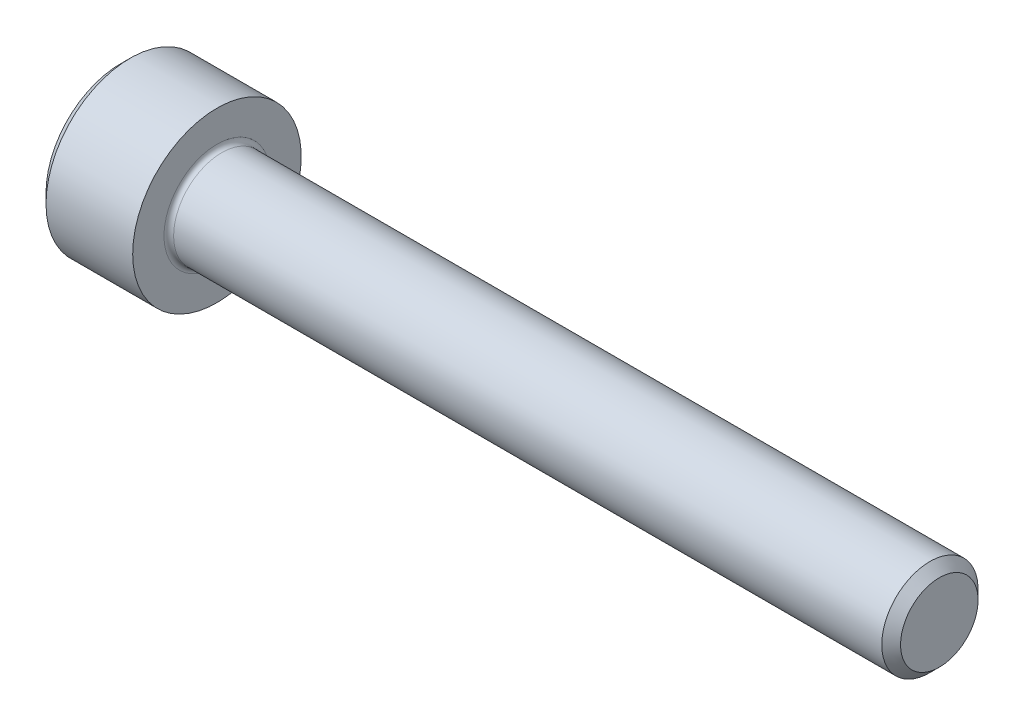
SolidWorks part; units mm, degrees
revolve "Base-Revolve" add sketch "BodySke"
sketch "BodySke" plane through (0, 0, 0) normal (0, 0, 1) x (1, 0, 0)
  line L0 (0, 0) -> (0, 3.1)
  line L1 (0.4, 3.5) -> (4, 3.5)
  line L2 (4, 3.5) -> (4, 2)
  line L3 (4, 2) -> (33.61, 2)
  line L4 (34, 1.61) -> (34, 0)
  line L5 (34, 0) -> (0, 0)
  line L6 (-31.75, 0) -> (127, 0) construction
  line L7 (0, 3.1) -> (0.4, 3.5)
  line L8 (34, 1.61) -> (33.61, 2)
  line L9 (0, -3.1) -> (0.4, -3.5) construction
  line L10 (34, -1.61) -> (33.61, -2) construction
  line L11 (4.7, 9.525) -> (4.7, 3.175) construction
  line L12 (4, 9.525) -> (4, 3.175) construction
  line L13 (-16, 9.525) -> (-16, 3.175) construction
  dimension "Diameter" = 4
  dimension "Head_ht" = 4
  dimension "Length" = 30
  dimension "Body_ch_ang" = 45
  dimension "Head_dia" = 7
  dimension "Head_ch_ang" = 45
  dimension "Minor_dia" = 3.22
  dimension "Advance" = 0.7
  dimension "Thread_nom" = 30
  dimension "Thread_length" = 50
  dimension "Head_ch_ht" = 0.4
cosmetic thread "ThreadCosmetic" [suppressed]
fillet "Fillet1" radius 0.2 1 edges at (4, 0, 2)
ref_plane "Plane1" through (0, 0, 0) normal (0, 0, 1) x (1, 0, 0)
ref_plane "Plane2" through (0, 0, 0) normal (0, 1, 0) x (1, 0, 0)
ref_plane "Plane3" through (0, 0, 0) normal (1, 0, 0) x (0, 0, -1)
other "Configuration Table"
sketch "Sketch2" plane through (0, 0, 0) normal (0, 0, 1) x (1, 0, 0)
  line L0 (0, 1.5355) -> (2, 1.5355)
  line L1 (2, 1.5355) -> (2.8865, 0)
  line L2 (-31.75, 0) -> (127, 0) construction
  line L3 (2.8865, 0) -> (0, 0)
  line L4 (0, 0) -> (0, 1.5355)
  line L5 (0, 3.1) -> (0, -3.1) construction
  line L6 (0, 0) -> (47.625, 0) construction
  line L7 (4, -3.5) -> (4, 3.5) construction
  dimension "D2" = 60
revolve "Hex-PreBroach" cut sketch "Sketch2" angle 360 about L6
sketch "Sketch3" plane through (0, 0, 0) normal (-1, 0, 0) x (0, 0.5, 0.866)
  line L0 (0.8865, 1.5355) -> (-0.8865, 1.5355)
  line L1 (-0.8865, 1.5355) -> (-1.773, 0)
  line L2 (0.8865, 1.5355) -> (1.773, 0)
  line L3 (0.8865, -1.5355) -> (1.773, 0)
  line L4 (0.8865, -1.5355) -> (-0.8865, -1.5355)
  line L5 (-0.8865, -1.5355) -> (-1.773, 0)
extrude "Hex" cut sketch "Sketch3" against normal blind 2
sketch "Sketch4" plane through (0, 0, 0) normal (-1, 0, 0) x (0, 0, 1)
  line L0 (0, 0) -> (1.7399, 0)
  line L1 (0, 0) -> (6.1484, 3.5498) construction
  line L2 (0, 0) -> (0.8699, 1.5068)
  line L3 (1.4457, 0.3947) -> (1.6607, 0.5189)
  line L4 (1.0647, 1.0546) -> (1.2797, 1.1788)
  arc A0 (1.4457, 0.3947) -> (1.0647, 1.0546) centre (0, 0) ccw
  arc A1 (1.7399, 0) -> (1.6607, 0.5189) centre (0, 0) ccw
  arc A2 (0.8699, 1.5068) -> (1.2797, 1.1788) centre (0, 0) cw
  dimension "D1" = 30
  dimension "D2" = 60
extrude "Spline" [suppressed] cut sketch "Sketch4" against normal blind 2
pattern_circular "CirPattern1" [suppressed] count 6 every 60
sketch "Sketch5" plane through (0, 0, 0) normal (0, 0, 1) x (1, 0, 0)
  line L0 (-31.75, 0) -> (127, 0) construction
  line L2 (0, 3.1) -> (0, -3.1) construction
  circle A0 centre (1.6, 0) radius 0.675
  dimension "Drilled_hole_dia" = 1.35
  dimension "Drilled_hole_loc" = 1.6
extrude "Hole" [suppressed] cut sketch "Sketch5" against normal through all and the other way through all
pattern_circular "Drilled-4" [suppressed] count 2 every 60
pattern_circular "Drilled-6" [suppressed] count 3 every 60
sketch "ThdSchSke" plane through (0, 0, 0) normal (0, 0, 1) x (1, 0, 0)
  line L0 (4.7, -1.61) -> (4.4269, -2)
  line L1 (4.7, -1.61) -> (4.9731, -2)
  line L2 (4.9731, -2) -> (4.9731, -2.5)
  line L3 (-3.175, 0) -> (5.1513, 0) construction
  line L5 (4.9731, -2.5) -> (4.4269, -2.5)
  line L6 (4.4269, -2.5) -> (4.4269, -2)
  line L7 (0, 3.1) -> (0, -3.1) construction
revolve "ThreadSchematic" [suppressed] cut sketch "ThdSchSke" angle 360 about L3
pattern_linear "ThdSchPat" [suppressed]
equation "\"D2@Sketch3\" = \"Hex_size@Sketch3\" / 2"
equation "\"D1@Sketch3\" = \"Hex_size@Sketch3\" / 2"
equation "\"D1@Sketch2\" = \"Hex_size@Sketch3\" / 2"
equation "\"D3@Sketch4\" = \"Spline_p_dim@Sketch4\" / 2"
equation "\"Thread_minor@ThreadCosmetic\"  =  \"Minor_dia@BodySke\""
equation "\"D2@CirPattern1\" = 360 / \"Num_teeth@CirPattern1\""
equation "\"Wall_thickness@Sketch2\" = \"Head_ht@BodySke\" - \"Key_eng@Hex\""
equation "\"Thread_length@ThreadCosmetic\" = ((sgn( (\"Length@BodySke\" - \"Advance@BodySke\" ) - \"Thread_nom@BodySke\" )-1)*( (\"Length@BodySke\" - \"Advance@BodySke\" ) - \"Thread_nom@BodySke\" ))/-2+ \"Thread_nom@BodySke\""
equation "\"Thread_minor@ThdSchSke\" = \"Minor_dia@BodySke\""
equation "\"Diameter@ThdSchSke\" = \"Diameter@BodySke\""
equation "\"Overcut@ThdSchSke\" = \"Diameter@BodySke\" * 1.25"
equation "\"Start@ThdSchSke\" = \"Head_ht@BodySke\" + \"Length@BodySke\" - \"Thread_length@ThreadCosmetic\"  '---Non-countersunk---"
equation "\"Num_threads@ThdSchPat\" = int( \"Thread_length@ThreadCosmetic\" / \"Advance@BodySke\" + 0.999 )  + 1"
equation "\"Advance@ThdSchPat\" = \"Thread_length@ThreadCosmetic\" /  (\"Num_threads@ThdSchPat\" - 1) 'relax it"
equation "\"Num_threads@ThdSchPat\" = \"Num_threads@ThdSchPat\" - sgn( \"Num_threads@ThdSchPat\" - 1) '---chamfered tips only---"
